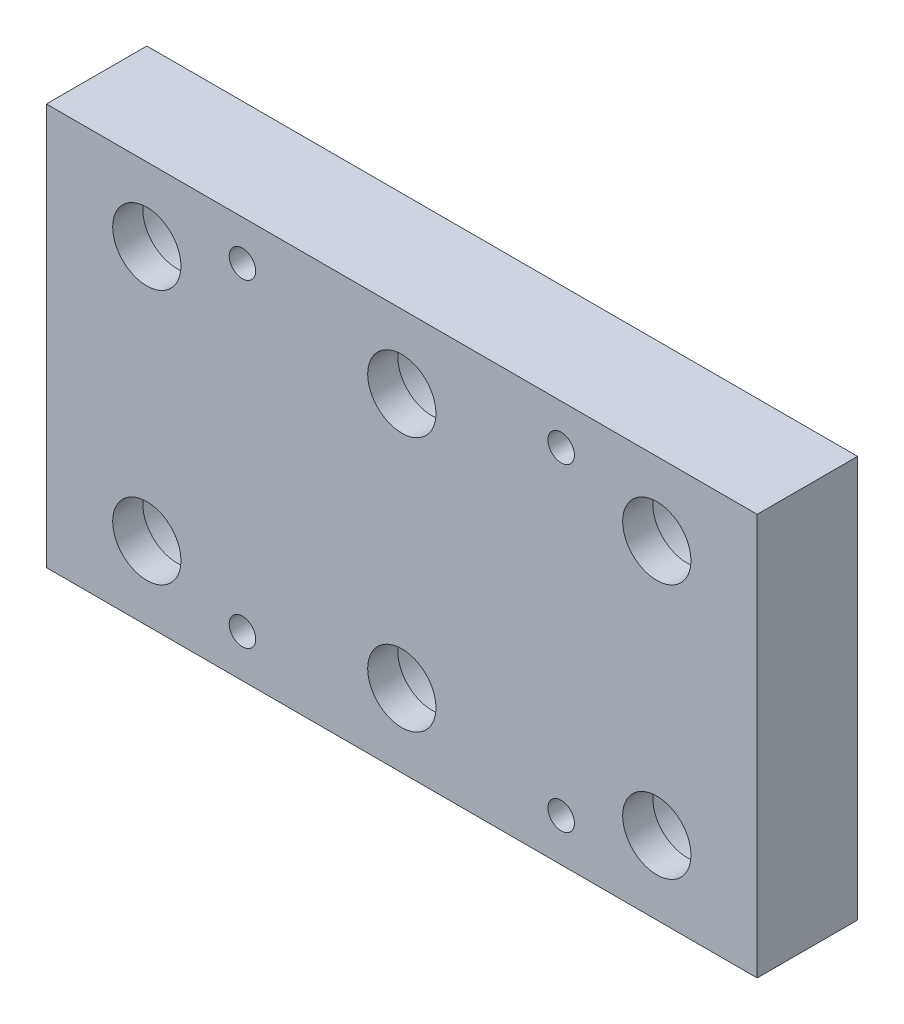
SolidWorks part; units mm, degrees
ref_plane "Front Plane" through (0, 0, 0) normal (0, 0, 1) x (1, 0, 0)
ref_plane "Top Plane" through (0, 0, 0) normal (0, 1, 0) x (1, 0, 0)
ref_plane "Right Plane" through (0, 0, 0) normal (1, 0, 0) x (0, 0, -1)
sketch "Sketch1" plane through (0, 0, 0) normal (0, 0, 1) x (1, 0, 0)
  line L0 (0, 20) -> (0, -20) construction
  line L1 (35.4, 20) -> (-35.4, 20)
  line L2 (35.4, 20) -> (35.4, -20)
  line L3 (35.4, -20) -> (-35.4, -20)
  line L4 (-35.4, 20) -> (-35.4, -20)
  line L5 (-35.4, 0) -> (35.4, 0) construction
  dimension "D1" = 70.8
  dimension "D2" = 40
extrude "Boss-Extrude1" add sketch "Sketch1" along normal blind 10
sketch "Sketch2" plane through (0, 0, 10) normal (0, 0, 1) x (1, 0, 0)
  line L0 (-15.875, -15.75) -> (15.875, -15.75) construction
  line L1 (15.875, -15.75) -> (15.875, 16) construction
  line L2 (15.875, 16) -> (-15.875, 16) construction
  line L4 (0, 0) -> (-35.4, 0) construction
  line L5 (-15.875, 16) -> (-15.875, -15.75) construction
  line L6 (0, 20) -> (0, -20) construction
  line L7 (35.4, 20) -> (-35.4, 20) construction
  line L8 (35.4, -20) -> (-35.4, -20) construction
  line L9 (-35.4, 20) -> (-35.4, -20) construction
  line L10 (35.4, 20) -> (35.4, -20) construction
  line L11 (-35.4, 0) -> (35.4, 0) construction
  line L12 (0, 16) -> (0, -15.75) construction
  circle A0 centre (15.875, -15.75) radius 1.32
  circle A1 centre (-15.875, -15.75) radius 1.32
  circle A2 centre (-15.875, 16) radius 1.32
  circle A3 centre (15.875, 16) radius 1.32
  dimension "D1" = 2.64
  dimension "D4" = 31.75
  dimension "D5" = 31.75
  dimension "D6" = 16
  dimension "D2" = 2
  dimension "D3" = 2
extrude "Cut-Extrude1" cut sketch "Sketch2" against normal through all
sketch "Sketch3" plane through (0, 0, 0) normal (0, 0, -1) x (-1, 0, 0)
  line L0 (-25.4, -12.7) -> (25.4, -12.7) construction
  line L1 (25.4, -12.7) -> (25.4, 12.7) construction
  line L2 (25.4, 12.7) -> (-25.4, 12.7) construction
  line L3 (-25.4, 12.7) -> (-25.4, -12.7) construction
  line L4 (-35.4, 20) -> (35.4, 20) construction
  line L5 (35.4, 20) -> (35.4, -20) construction
  line L6 (35.4, -20) -> (-35.4, -20) construction
  line L7 (-35.4, -20) -> (-35.4, 20) construction
  line L8 (0, -20) -> (0, 20) construction
  line L9 (35.4, 0) -> (-35.4, 0) construction
  circle A0 centre (-25.4, -12.7) radius 3.4
  circle A1 centre (0, -12.7) radius 3.4
  circle A2 centre (25.4, -12.7) radius 3.4
  circle A4 centre (0, 12.7) radius 3.4
  circle A5 centre (25.4, 12.7) radius 3.4
  circle A7 centre (-25.4, 12.7) radius 3.4
  dimension "D1" = 6.8
  dimension "D6" = 12.7
  dimension "D4" = 25.4
  dimension "D5" = 50.8
  dimension "D2" = 3
  dimension "D3" = 2
extrude "Cut-Extrude2" cut sketch "Sketch3" against normal through all
sketch "Sketch4" plane through (0, 0, 0) normal (0, 0, -1) x (-1, 0, 0)
  line L0 (-35.4, 0) -> (35.4, 0) construction
  line L1 (35.4, 0) -> (-35.4, 0) construction
  circle A0 centre (25.4, -12.7) radius 5.375
  circle A1 centre (0, -12.7) radius 5.375
  circle A2 centre (-25.4, -12.7) radius 5.375
  circle A3 centre (0, 12.7) radius 5.375
  circle A4 centre (-25.4, 12.7) radius 5.375
  circle A5 centre (25.4, 12.7) radius 5.375
  circle A6 centre (0, 12.7) radius 3.4 construction
  circle A7 centre (-25.4, 12.7) radius 3.4 construction
  dimension "D1" = 10.75
  dimension "D4" = 10
  dimension "D5" = 10
  dimension "D6" = 70.8
  dimension "D2" = 3
  dimension "D3" = 2
extrude "Cut-Extrude3" cut sketch "Sketch4" against normal blind 7
equation "\"hole_screw_1_4_20\"= 6"
equation "\"inch\"=25.43"
